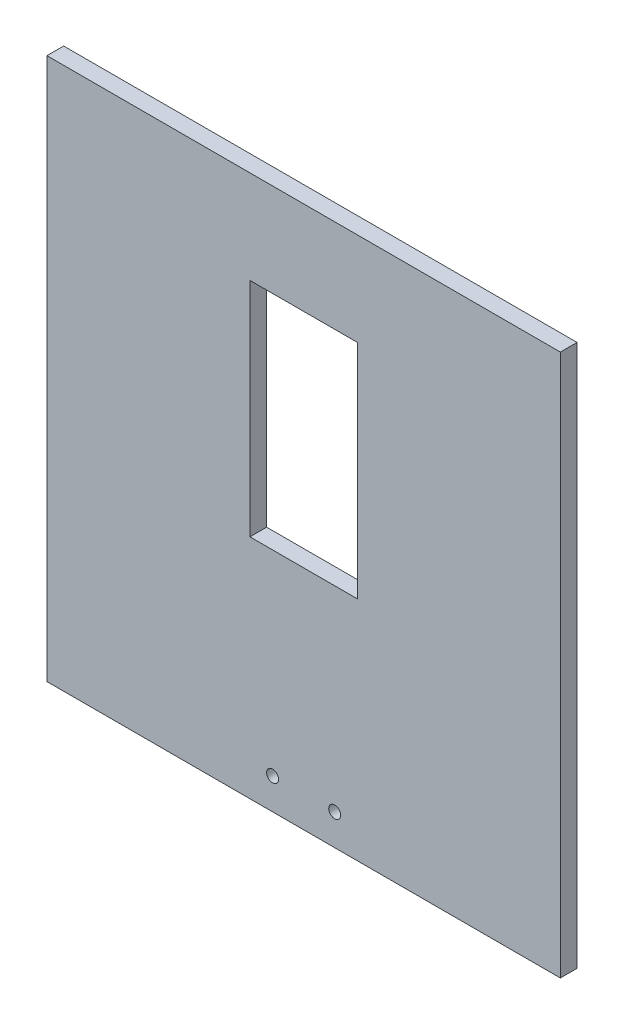
SolidWorks part; units mm, degrees
ref_plane "Front Plane" through (0, 0, 0) normal (0, 0, 1) x (1, 0, 0)
ref_plane "Top Plane" through (0, 0, 0) normal (0, 1, 0) x (1, 0, 0)
ref_plane "Right Plane" through (0, 0, 0) normal (1, 0, 0) x (0, 0, -1)
sketch "Sketch1" plane through (0, 0, 0) normal (0, 0, 1) x (1, 0, 0)
  line L1 (-107.5, -110.4106) -> (107.5, -110.4106)
  line L2 (-107.5, -110.4106) -> (-107.5, 116.5894)
  line L3 (-107.5, 116.5894) -> (107.5, 116.5894)
  line L4 (107.5, -110.4106) -> (107.5, 116.5894)
  line L5 (-22.5, 77.5894) -> (22.5, 77.5894)
  line L6 (-22.5, 77.5894) -> (-22.5, -15.4106)
  line L7 (-22.5, -15.4106) -> (22.5, -15.4106)
  line L8 (22.5, 77.5894) -> (22.5, -15.4106)
  circle A0 centre (-13, -97.4106) radius 2.5
  circle A1 centre (13, -97.4106) radius 2.5
  point P0 (0, 0)
  point P6 (0, 31.0894)
  point P11 (0, 116.5894)
  point P13 (0, 77.5894)
  dimension "D6" = 26
  dimension "D1" = 215
  dimension "D2" = 227
  dimension "D3" = 95
  dimension "D4" = 93
  dimension "D5" = 45
  dimension "D7" = 13
  dimension "D8" = 13
extrude "Boss-Extrude1" add sketch "Sketch1" along normal blind 7 contours L1 L4 L3 L2 L5 L8 L7 L6
